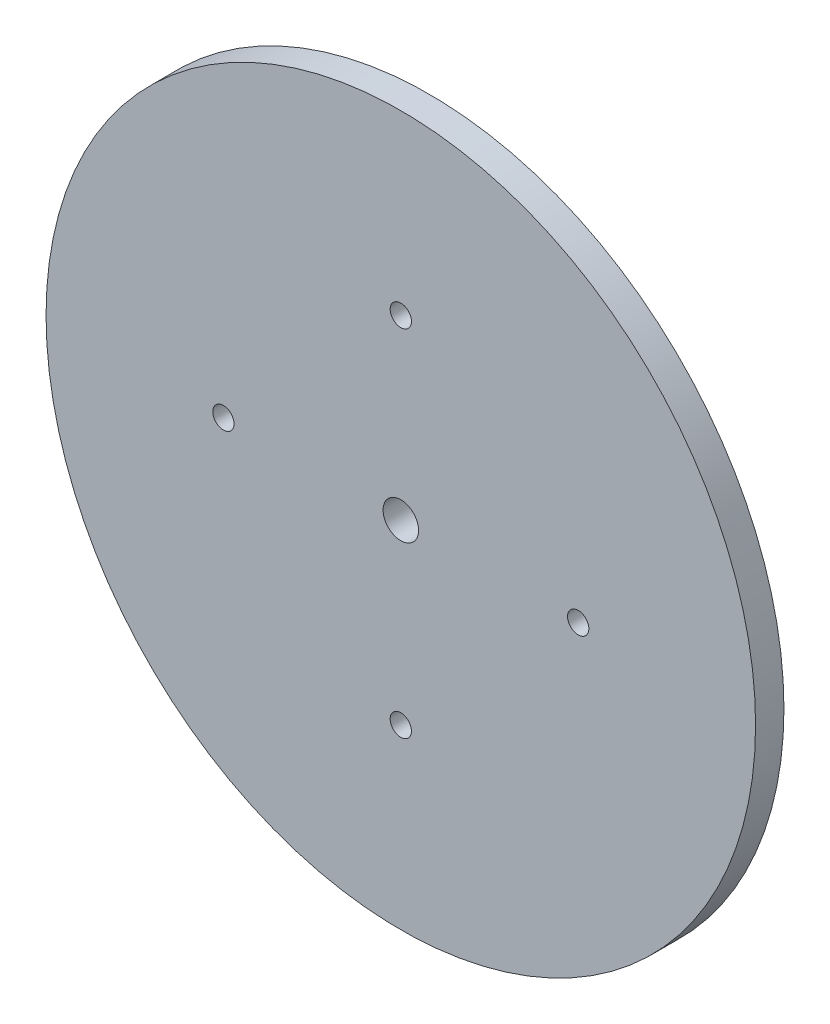
SolidWorks part; units mm, degrees
ref_plane "Front Plane" through (0, 0, 0) normal (0, 0, 1) x (1, 0, 0)
ref_plane "Top Plane" through (0, 0, 0) normal (0, 1, 0) x (1, 0, 0)
ref_plane "Right Plane" through (0, 0, 0) normal (1, 0, 0) x (0, 0, -1)
sketch "Sketch1" plane through (0, 0, 0) normal (0, 0, 1) x (1, 0, 0)
  circle A0 centre (-42.2867, 29.939) radius 50
  dimension "D1" = 100
extrude "Boss-Extrude1" add sketch "Sketch1" along normal blind 4 contours A0
sketch "Sketch4" plane through (0, 0, 4) normal (0, 0, 1) x (1, 0, 0)
  circle A1 centre (-42.2867, 29.939) radius 2.5
extrude "Cut-Extrude1" cut sketch "Sketch4" against normal blind 5
sketch "Sketch5" plane through (0, 0, 4) normal (0, 0, 1) x (1, 0, 0)
  circle A1 centre (-67.2867, 29.939) radius 1.5
  circle A2 centre (-42.2867, 54.939) radius 1.5
  circle A3 centre (-17.2867, 29.939) radius 1.5
  circle A4 centre (-42.2867, 4.939) radius 1.5
  point P11 (-42.2867, 29.939)
  dimension "D1" = 4
extrude "Cut-Extrude2" cut sketch "Sketch5" against normal blind 4
